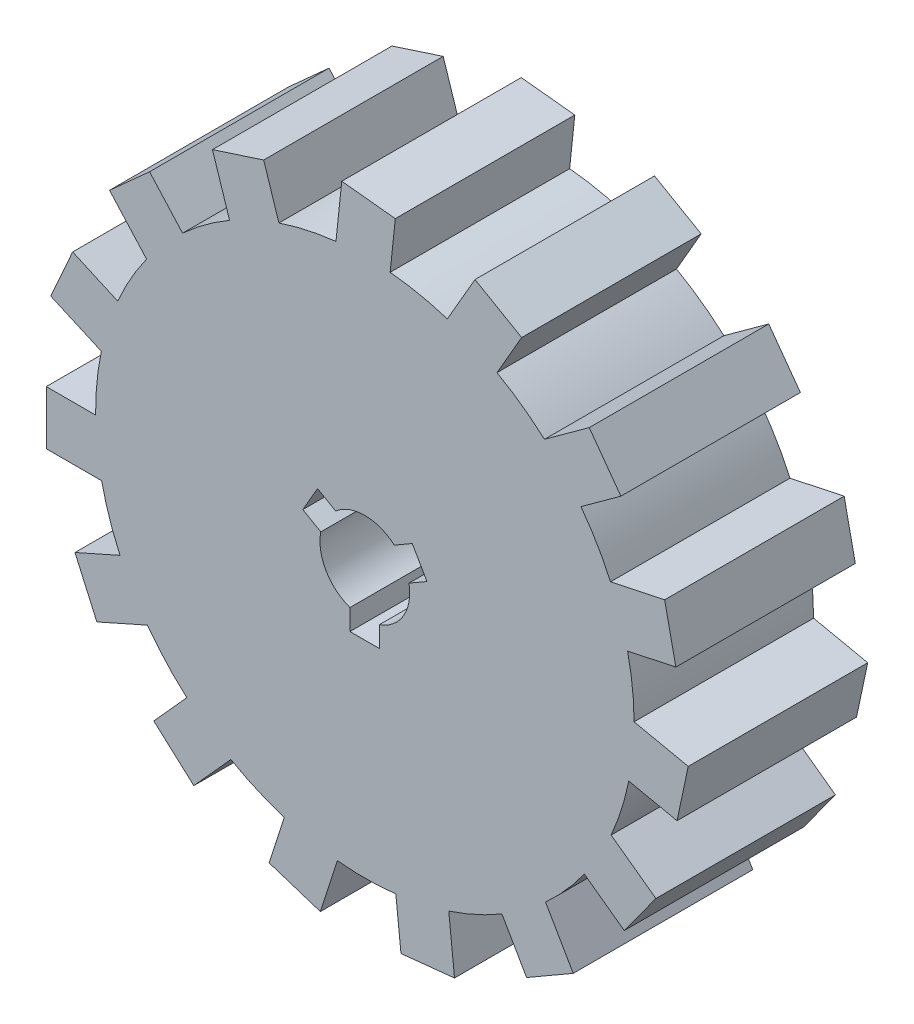
SolidWorks part; units mm, degrees
ref_plane "Front Plane" through (0, 0, 0) normal (0, 0, 1) x (1, 0, 0)
ref_plane "Top Plane" through (0, 0, 0) normal (0, 1, 0) x (1, 0, 0)
ref_plane "Right Plane" through (0, 0, 0) normal (1, 0, 0) x (0, 0, -1)
ref_plane "Plane4"
sketch "Sketch1" plane through (0, 0, 0) normal (0, 0, 1) x (1, 0, 0)
  line L0 (21.2133, 8.6105) -> (17.3817, 7.7961)
  line L1 (15.2923, 11.36) -> (18.1166, 13.4119)
  line L2 (18.1166, 13.4119) -> (15.8771, 16.4943)
  line L3 (15.8771, 16.4943) -> (12.708, 14.1918)
  line L4 (9.3497, 16.5978) -> (11.0952, 19.6211)
  line L5 (11.0952, 19.6211) -> (7.7956, 21.5261)
  line L6 (7.7956, 21.5261) -> (5.837, 18.1337)
  line L7 (-19.0489, -0.2018) -> (-22.54, -0.2018)
  line L8 (-22.54, -0.2018) -> (-22.54, -4.0118)
  line L9 (-22.54, -4.0118) -> (-18.6228, -4.0118)
  line L10 (-17.32, -7.9323) -> (-20.5092, -9.3522)
  line L11 (-20.5092, -9.3522) -> (-18.9595, -12.8328)
  line L12 (-18.9595, -12.8328) -> (-15.381, -11.2396)
  line L13 (-12.5962, -14.2912) -> (-14.9322, -16.8855)
  line L14 (-14.9322, -16.8855) -> (-12.1008, -19.4349)
  line L15 (-12.1008, -19.4349) -> (-9.4797, -16.5239)
  line L16 (-5.6945, -18.179) -> (-6.7733, -21.4991)
  line L17 (-6.7733, -21.4991) -> (-3.1497, -22.6765)
  line L18 (-3.1497, -22.6765) -> (-1.9393, -18.951)
  line L19 (2.1919, -18.9235) -> (2.5568, -22.3954)
  line L20 (2.5568, -22.3954) -> (6.3459, -21.9971)
  line L21 (6.3459, -21.9971) -> (5.9365, -18.1014)
  line L22 (9.6993, -16.3959) -> (11.4448, -19.4193)
  line L23 (11.4448, -19.4193) -> (14.7443, -17.5143)
  line L24 (14.7443, -17.5143) -> (12.7857, -14.1219)
  line L25 (15.5295, -11.0334) -> (18.3538, -13.0854)
  line L26 (18.3538, -13.0854) -> (20.5933, -10.003)
  line L27 (20.5933, -10.003) -> (17.4242, -7.7006)
  line L28 (18.6746, -3.7631) -> (22.0894, -4.4889)
  line L29 (22.0894, -4.4889) -> (22.8815, -0.7622)
  line L30 (22.8815, -0.7622) -> (19.0499, 0.0523)
  line L31 (18.5907, 4.1579) -> (22.0054, 4.8837)
  line L32 (22.0054, 4.8837) -> (21.2133, 8.6105)
  line L33 (-3.3435, 3.1468) -> (-2.0672, 2.4099)
  line L34 (2.0833, 2.3959) -> (3.3536, 3.1294)
  line L35 (3.3536, 3.1294) -> (4.397, 1.3222)
  line L36 (4.397, 1.3222) -> (3.1206, 0.5853)
  line L37 (1.0333, -3.0022) -> (1.0333, -4.469)
  line L38 (1.0333, -4.469) -> (-1.0534, -4.469)
  line L39 (-1.0534, -4.469) -> (-1.0534, -2.9952)
  line L40 (-3.1166, 0.6062) -> (-4.3869, 1.3396)
  line L41 (-4.3869, 1.3396) -> (-3.3435, 3.1468)
  line L42 (-1.6338, 22.8358) -> (-2.0432, 18.9401)
  line L43 (1.7904, 18.9657) -> (2.1553, 22.4376)
  line L44 (2.1553, 22.4376) -> (-1.6338, 22.8358)
  line L45 (-10.7807, 20.197) -> (-9.5702, 16.4716)
  line L46 (-6.0784, 18.0542) -> (-7.1572, 21.3744)
  line L47 (-7.1572, 21.3744) -> (-10.7807, 20.197)
  line L48 (-18.0635, 14.066) -> (-15.4424, 11.155)
  line L49 (-12.8962, 14.0211) -> (-15.2322, 16.6154)
  line L50 (-15.2322, 16.6154) -> (-18.0635, 14.066)
  line L51 (-22.223, 5.5028) -> (-18.6445, 3.9096)
  line L52 (-17.4842, 7.5635) -> (-20.6734, 8.9834)
  line L53 (-20.6734, 8.9834) -> (-22.223, 5.5028)
  arc A0 (17.3817, 7.7961) -> (15.2923, 11.36) centre (0, 0) ccw
  arc A1 (12.708, 14.1918) -> (9.3497, 16.5978) centre (0, 0) ccw
  arc A2 (5.837, 18.1337) -> (-19.0489, -0.2018) centre (0, 0) ccw
  arc A3 (-18.6228, -4.0118) -> (-17.32, -7.9323) centre (0, 0) ccw
  arc A4 (-15.381, -11.2396) -> (-12.5962, -14.2912) centre (0, 0) ccw
  arc A5 (-9.4797, -16.5239) -> (-5.6945, -18.179) centre (0, 0) ccw
  arc A6 (-1.9393, -18.951) -> (2.1919, -18.9235) centre (0, 0) ccw
  arc A7 (5.9365, -18.1014) -> (9.6993, -16.3959) centre (0, 0) ccw
  arc A8 (12.7857, -14.1219) -> (15.5295, -11.0334) centre (0, 0) ccw
  arc A9 (17.4242, -7.7006) -> (18.6746, -3.7631) centre (0, 0) ccw
  arc A10 (19.0499, 0.0523) -> (18.5907, 4.1579) centre (0, 0) ccw
  arc A11 (2.0833, 2.3959) -> (-2.0672, 2.4099) centre (0, 0) ccw
  arc A12 (1.0333, -3.0022) -> (3.1206, 0.5853) centre (0, 0) ccw
  arc A13 (-3.1166, 0.6062) -> (-1.0534, -2.9952) centre (0, 0) ccw
  arc A14 (1.7904, 18.9657) -> (-2.0432, 18.9401) centre (0, 0) ccw
  arc A15 (-6.0784, 18.0542) -> (-9.5702, 16.4716) centre (0, 0) ccw
  arc A16 (-12.8962, 14.0211) -> (-15.4424, 11.155) centre (0, 0) ccw
  arc A17 (-17.4842, 7.5635) -> (-18.6445, 3.9096) centre (0, 0) ccw
  dimension "D1" = 3.81
  dimension "D2" = 5.7135
  dimension "D3" = 22.5409
extrude "Extrusion3" add sketch "Sketch1" along normal blind 12.7 contours L30 A10 L31 L32 L0 A0 L1 L2 L3 A1 L4 L5 L6 A2 L7 L8 L9 A3 L10 L11 L12 A4 L13 L14 L15 A5 L16 L17 L18 A6 L19 L20 L21 A7 L22 L23 L24 A8 L25 L26 L27 A9 L28 | A2 L43 L44 L42 | A2 L46 L47 L45 | A2 L49 L50 L48 | A2 L52 L53 L51
